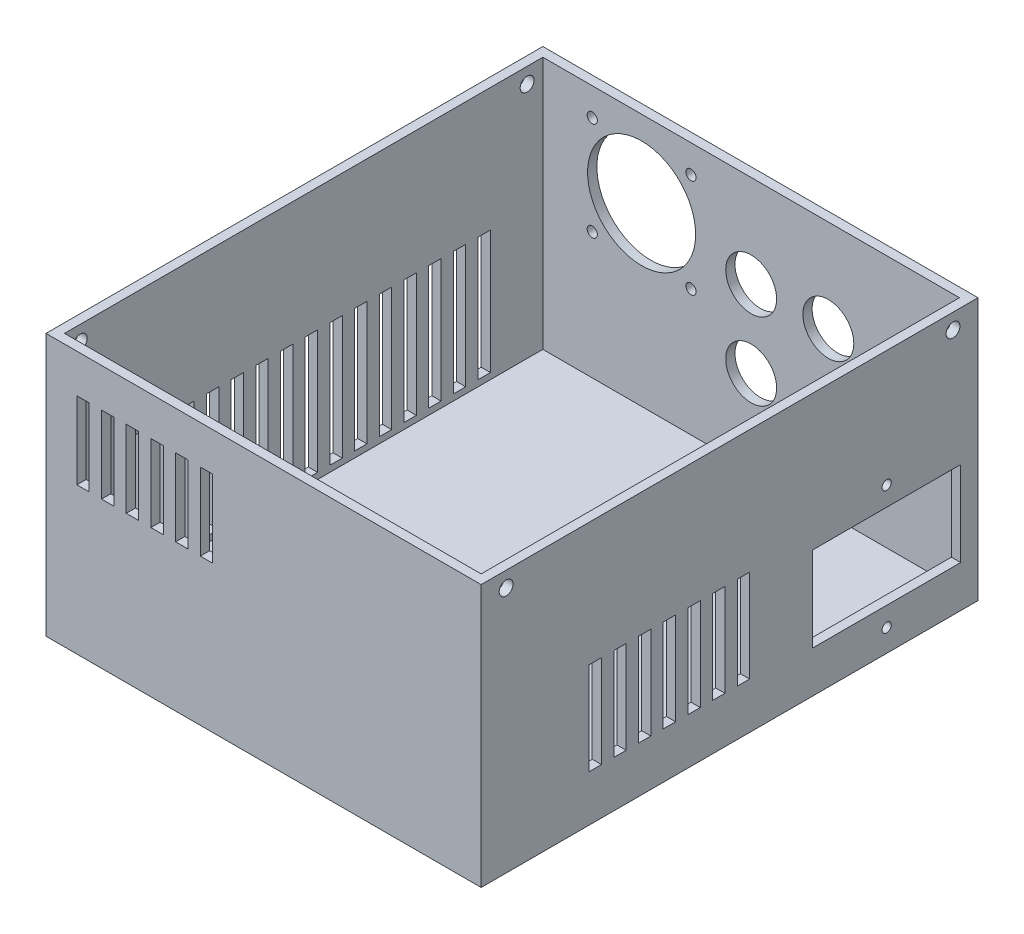
SolidWorks part; units mm, degrees
ref_plane "Front Plane" through (0, 0, 0) normal (0, 0, 1) x (1, 0, 0)
ref_plane "Top Plane" through (0, 0, 0) normal (0, 1, 0) x (1, 0, 0)
ref_plane "Right Plane" through (0, 0, 0) normal (1, 0, 0) x (0, 0, -1)
sketch "Sketch1" plane through (0, 0, 0) normal (0, 1, 0) x (1, 0, 0)
  line L1 (-67.5, -77.5) -> (67.5, -77.5)
  line L2 (-67.5, -77.5) -> (-67.5, 77.5)
  line L3 (-67.5, 77.5) -> (67.5, 77.5)
  line L4 (67.5, -77.5) -> (67.5, 77.5)
  line L5 (-67.5, -77.5) -> (67.5, 77.5) construction
  line L6 (-67.5, 77.5) -> (67.5, -77.5) construction
  point P0 (0, 0)
  dimension "D1" = 135
  dimension "D2" = 155
extrude "Boss-Extrude1" add sketch "Sketch1" along normal blind 3
sketch "Sketch3" plane through (0, 0, 0) normal (0, 1, 0) x (1, 0, 0)
  line L1 (67.5, -77.5) -> (-67.5, -77.5)
  line L2 (67.5, -77.5) -> (67.5, 77.5)
  line L3 (67.5, 77.5) -> (-67.5, 77.5)
  line L4 (-67.5, -77.5) -> (-67.5, 77.5)
  line L5 (-70.5, -80.5) -> (70.5, -80.5)
  line L6 (-70.5, -80.5) -> (-70.5, 80.5)
  line L7 (-70.5, 80.5) -> (70.5, 80.5)
  line L8 (70.5, -80.5) -> (70.5, 80.5)
  line L9 (-70.5, -80.5) -> (70.5, 80.5) construction
  line L10 (-70.5, 80.5) -> (70.5, -80.5) construction
  point P6 (0, 0)
  dimension "D1" = 3
  dimension "D2" = 3
extrude "Boss-Extrude3" add sketch "Sketch3" along normal blind 85
sketch "Sketch4" plane through (-70.5, 0, 0) normal (-1, 0, 0) x (0, 0, 1)
  line L0 (-80.5, 0) -> (80.5, 0) construction
  line L1 (-48.5, 5) -> (-48.5, 45)
  line L2 (-48.5, 5) -> (-52.5, 5)
  line L3 (-56.5, 5) -> (-60.5, 5)
  line L4 (-56.5, 5) -> (-56.5, 45)
  line L5 (-56.5, 45) -> (-60.5, 45)
  line L6 (-60.5, 5) -> (-60.5, 45)
  line L7 (-56.5, 5) -> (-60.5, 45) construction
  line L8 (-56.5, 45) -> (-60.5, 5) construction
  line L9 (-80.5, 85) -> (-80.5, 0) construction
  line L10 (-52.5, 5) -> (-52.5, 45)
  line L11 (-48.5, 45) -> (-52.5, 45)
  line L12 (-40.5, 5) -> (-40.5, 45)
  line L13 (-40.5, 5) -> (-44.5, 5)
  line L14 (-44.5, 5) -> (-44.5, 45)
  line L15 (-40.5, 45) -> (-44.5, 45)
  line L16 (-32.5, 5) -> (-32.5, 45)
  line L17 (-32.5, 5) -> (-36.5, 5)
  line L18 (-36.5, 5) -> (-36.5, 45)
  line L19 (-32.5, 45) -> (-36.5, 45)
  line L20 (-24.5, 5) -> (-24.5, 45)
  line L21 (-24.5, 5) -> (-28.5, 5)
  line L22 (-28.5, 5) -> (-28.5, 45)
  line L23 (-24.5, 45) -> (-28.5, 45)
  line L24 (-16.5, 5) -> (-16.5, 45)
  line L25 (-16.5, 5) -> (-20.5, 5)
  line L26 (-20.5, 5) -> (-20.5, 45)
  line L27 (-16.5, 45) -> (-20.5, 45)
  line L28 (-8.5, 5) -> (-8.5, 45)
  line L29 (-8.5, 5) -> (-12.5, 5)
  line L30 (-12.5, 5) -> (-12.5, 45)
  line L31 (-8.5, 45) -> (-12.5, 45)
  line L32 (-0.5, 5) -> (-0.5, 45)
  line L33 (-0.5, 5) -> (-4.5, 5)
  line L34 (-4.5, 5) -> (-4.5, 45)
  line L35 (-0.5, 45) -> (-4.5, 45)
  line L36 (7.5, 5) -> (7.5, 45)
  line L37 (7.5, 5) -> (3.5, 5)
  line L38 (3.5, 5) -> (3.5, 45)
  line L39 (7.5, 45) -> (3.5, 45)
  line L40 (15.5, 5) -> (15.5, 45)
  line L41 (15.5, 5) -> (11.5, 5)
  line L42 (11.5, 5) -> (11.5, 45)
  line L43 (15.5, 45) -> (11.5, 45)
  line L44 (23.5, 5) -> (23.5, 45)
  line L45 (23.5, 5) -> (19.5, 5)
  line L46 (19.5, 5) -> (19.5, 45)
  line L47 (23.5, 45) -> (19.5, 45)
  line L48 (31.5, 5) -> (31.5, 45)
  line L49 (31.5, 5) -> (27.5, 5)
  line L50 (27.5, 5) -> (27.5, 45)
  line L51 (31.5, 45) -> (27.5, 45)
  line L52 (39.5, 5) -> (39.5, 45)
  line L53 (39.5, 5) -> (35.5, 5)
  line L54 (35.5, 5) -> (35.5, 45)
  line L55 (39.5, 45) -> (35.5, 45)
  line L56 (47.5, 5) -> (47.5, 45)
  line L57 (47.5, 5) -> (43.5, 5)
  line L58 (43.5, 5) -> (43.5, 45)
  line L59 (47.5, 45) -> (43.5, 45)
  line L60 (55.5, 5) -> (55.5, 45)
  line L61 (55.5, 5) -> (51.5, 5)
  line L62 (51.5, 5) -> (51.5, 45)
  line L63 (55.5, 45) -> (51.5, 45)
  point P0 (-58.5, 25)
  dimension "D1" = 4
  dimension "D2" = 5
  dimension "D3" = 20
  dimension "D4" = 40
  dimension "D6" = 4
  dimension "D5" = 15
extrude "Cut-Extrude1" cut sketch "Sketch4" against normal up to next
sketch "Sketch5" plane through (0, 0, -80.5) normal (0, 0, 1) x (1, 0, 0)
  line L0 (-55.5, 80) -> (-55.5, 40) construction
  line L1 (-55.5, 40) -> (-15.5, 40) construction
  line L2 (-15.5, 40) -> (-15.5, 80) construction
  line L3 (-15.5, 80) -> (-55.5, 80) construction
  line L4 (-70.5, 85) -> (-70.5, 0) construction
  line L5 (70.5, 85) -> (-70.5, 85) construction
  line L6 (-35.5, 40) -> (-35.5, 80) construction
  line L7 (-55.5, 60) -> (-15.5, 60) construction
  circle A0 centre (-35.5, 60) radius 17.5
  circle A1 centre (-51.5, 44) radius 1.65
  circle A2 centre (-19.5, 44) radius 1.65
  circle A3 centre (-19.5, 76) radius 1.65
  circle A4 centre (-51.5, 76) radius 1.65
  dimension "D5" = 35
  dimension "D6" = 3.3
  dimension "D7" = 16
  dimension "D8" = 16
  dimension "D1" = 40
  dimension "D2" = 40
  dimension "D3" = 15
  dimension "D4" = 5
extrude "Cut-Extrude2" cut sketch "Sketch5" along normal up to next
sketch "Sketch6" plane through (70.5, 0, 0) normal (1, 0, 0) x (0, 0, -1)
  line L0 (80.5, 85) -> (80.5, 0) construction
  line L1 (74.9, 41) -> (26.9, 41)
  line L2 (74.9, 41) -> (74.9, 13.5)
  line L3 (74.9, 13.5) -> (26.9, 13.5)
  line L4 (26.9, 41) -> (26.9, 13.5)
  line L5 (-80.5, 85) -> (80.5, 85) construction
  line L6 (26.9, 27.25) -> (74.9, 27.25) construction
  line L7 (50.9, 27.25) -> (50.9, 47.25) construction
  circle A0 centre (50.9, 47.25) radius 1.5
  circle A1 centre (50.9, 7.25) radius 1.5
  dimension "D5" = 3
  dimension "D1" = 5.6
  dimension "D2" = 48
  dimension "D3" = 27.5
  dimension "D4" = 44
  dimension "D6" = 20
extrude "Cut-Extrude3" cut sketch "Sketch6" against normal up to next and the other way through all
sketch "Sketch7" plane through (0, 0, -80.5) normal (0, 0, -1) x (-1, 0, 0)
  line L0 (0, 0) -> (0, 85) construction
  line L1 (-70.5, 85) -> (70.5, 85) construction
  line L2 (-70.5, 42.5) -> (0, 42.5) construction
  line L3 (-70.5, 85) -> (-70.5, 0) construction
  circle A0 centre (0, 55) radius 8.25
  circle A1 centre (-25, 55) radius 8.25
  circle A2 centre (0, 30) radius 8.25
  circle A3 centre (-25, 30) radius 8.25
  dimension "D1" = 16.5
  dimension "D2" = 0
  dimension "D3" = 12.5
  dimension "D5" = 25
  dimension "D4" = 2
extrude "Cut-Extrude4" cut sketch "Sketch7" against normal up to next
sketch "Sketch8" plane through (70.5, 0, 0) normal (1, 0, 0) x (0, 0, -1)
  line L0 (-80.5, 30) -> (26.9, 30) construction
  line L3 (-80.5, 85) -> (-80.5, 0) construction
  line L4 (26.9, 41) -> (26.9, 13.5) construction
  line L5 (-80.5, 0) -> (80.5, 0) construction
  line L6 (-37.5, 15) -> (-37.5, 45)
  line L7 (-45.5, 15) -> (-41.5, 15)
  line L8 (-45.5, 15) -> (-45.5, 45)
  line L9 (-45.5, 45) -> (-41.5, 45)
  line L10 (-41.5, 15) -> (-41.5, 45)
  line L11 (-45.5, 15) -> (-41.5, 45) construction
  line L12 (-45.5, 45) -> (-41.5, 15) construction
  line L13 (-37.5, 15) -> (-33.5, 15)
  line L14 (-33.5, 15) -> (-33.5, 45)
  line L15 (-37.5, 45) -> (-33.5, 45)
  line L16 (-29.5, 15) -> (-29.5, 45)
  line L17 (-29.5, 15) -> (-25.5, 15)
  line L18 (-25.5, 15) -> (-25.5, 45)
  line L19 (-29.5, 45) -> (-25.5, 45)
  line L20 (-21.5, 15) -> (-21.5, 45)
  line L21 (-21.5, 15) -> (-17.5, 15)
  line L22 (-17.5, 15) -> (-17.5, 45)
  line L23 (-21.5, 45) -> (-17.5, 45)
  line L24 (-13.5, 15) -> (-13.5, 45)
  line L25 (-13.5, 15) -> (-9.5, 15)
  line L26 (-9.5, 15) -> (-9.5, 45)
  line L27 (-13.5, 45) -> (-9.5, 45)
  line L28 (-5.5, 15) -> (-5.5, 45)
  line L29 (-5.5, 15) -> (-1.5, 15)
  line L30 (-1.5, 15) -> (-1.5, 45)
  line L31 (-5.5, 45) -> (-1.5, 45)
  line L32 (2.5, 15) -> (2.5, 45)
  line L33 (2.5, 15) -> (6.5, 15)
  line L34 (6.5, 15) -> (6.5, 45)
  line L35 (2.5, 45) -> (6.5, 45)
  point P8 (-43.5, 30)
  dimension "D1" = 30
  dimension "D2" = 30
  dimension "D3" = 4
  dimension "D4" = 35
  dimension "D6" = 4
  dimension "D5" = 7
extrude "Cut-Extrude5" cut sketch "Sketch8" against normal up to next
sketch "Sketch9" plane through (0, 0, 80.5) normal (0, 0, 1) x (1, 0, 0)
  line L0 (-70.5, 60) -> (70.5, 60) construction
  line L1 (-70.5, 85) -> (-70.5, 0) construction
  line L2 (70.5, 85) -> (70.5, 0) construction
  line L3 (-70.5, 85) -> (70.5, 85) construction
  line L4 (-52.5, 47.5) -> (-52.5, 72.5)
  line L5 (-60.5, 47.5) -> (-56.5, 47.5)
  line L6 (-60.5, 47.5) -> (-60.5, 72.5)
  line L7 (-60.5, 72.5) -> (-56.5, 72.5)
  line L8 (-56.5, 47.5) -> (-56.5, 72.5)
  line L9 (-60.5, 47.5) -> (-56.5, 72.5) construction
  line L10 (-60.5, 72.5) -> (-56.5, 47.5) construction
  line L11 (-52.5, 47.5) -> (-48.5, 47.5)
  line L12 (-48.5, 47.5) -> (-48.5, 72.5)
  line L13 (-52.5, 72.5) -> (-48.5, 72.5)
  line L14 (-44.5, 47.5) -> (-44.5, 72.5)
  line L15 (-44.5, 47.5) -> (-40.5, 47.5)
  line L16 (-40.5, 47.5) -> (-40.5, 72.5)
  line L17 (-44.5, 72.5) -> (-40.5, 72.5)
  line L18 (-36.5, 47.5) -> (-36.5, 72.5)
  line L19 (-36.5, 47.5) -> (-32.5, 47.5)
  line L20 (-32.5, 47.5) -> (-32.5, 72.5)
  line L21 (-36.5, 72.5) -> (-32.5, 72.5)
  line L22 (-28.5, 47.5) -> (-28.5, 72.5)
  line L23 (-28.5, 47.5) -> (-24.5, 47.5)
  line L24 (-24.5, 47.5) -> (-24.5, 72.5)
  line L25 (-28.5, 72.5) -> (-24.5, 72.5)
  line L26 (-20.5, 47.5) -> (-20.5, 72.5)
  line L27 (-20.5, 47.5) -> (-16.5, 47.5)
  line L28 (-16.5, 47.5) -> (-16.5, 72.5)
  line L29 (-20.5, 72.5) -> (-16.5, 72.5)
  point P8 (-58.5, 60)
  dimension "D1" = 25
  dimension "D2" = 4
  dimension "D3" = 25
  dimension "D4" = 10
  dimension "D6" = 4
  dimension "D5" = 6
extrude "Cut-Extrude6" cut sketch "Sketch9" against normal up to next
sketch "Sketch11" plane through (-70.5, 0, 0) normal (-1, 0, 0) x (0, 0, 1)
  line L0 (-80.5, 85) -> (80.5, 85) construction
  line L1 (-80.5, 85) -> (-80.5, 0) construction
  line L2 (0, 0) -> (0, 85) construction
  line L3 (-80.5, 0) -> (80.5, 0) construction
  circle A0 centre (-72.4, 80) radius 2.25
  circle A1 centre (72.4, 80) radius 2.25
  dimension "D1" = 5
  dimension "D2" = 8.1
  dimension "D3" = 4.5
extrude "Cut-Extrude7" cut sketch "Sketch11" against normal through all
